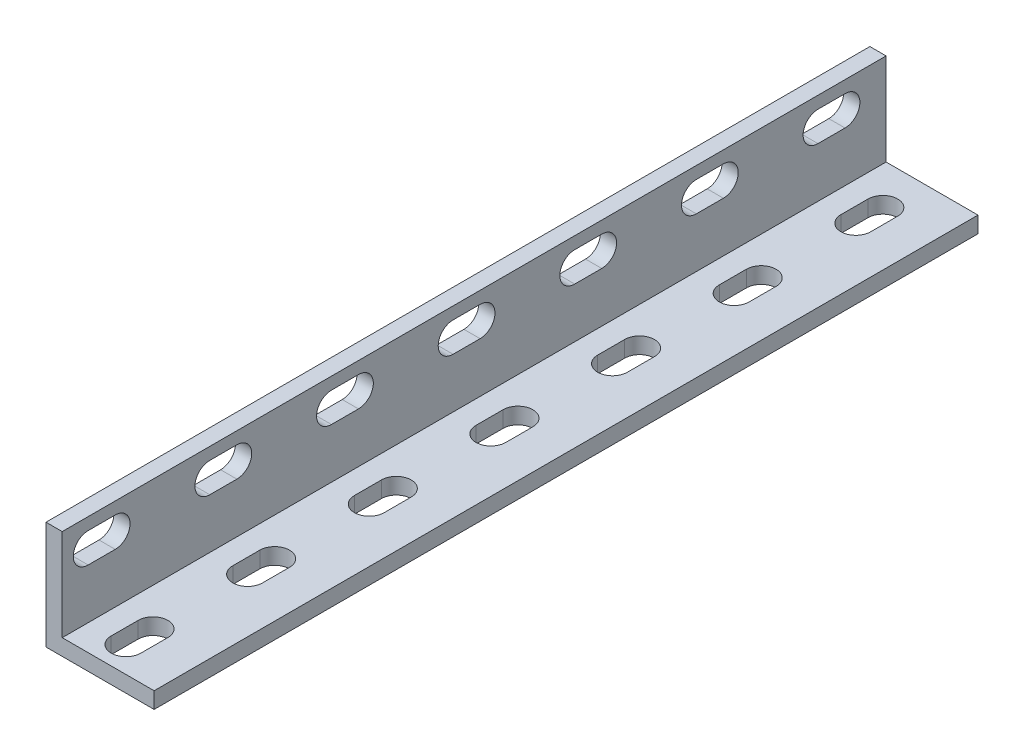
SolidWorks part; units mm, degrees
material "6061 Alloy"
ref_plane "Front Plane" through (0, 0, 0) normal (0, 0, 1) x (1, 0, 0)
ref_plane "Top Plane" through (0, 0, 0) normal (0, 1, 0) x (1, 0, 0)
ref_plane "Right Plane" through (0, 0, 0) normal (1, 0, 0) x (0, 0, -1)
sketch "Sketch1" plane through (0, 0, 0) normal (0, 0, 1) x (1, 0, 0)
  line L0 (0, 20) -> (0, 0)
  line L1 (0, 0) -> (20, 0)
  dimension "D1" = 20
  dimension "D2" = 20
extrude "Extrude-Thin1" add sketch "Sketch1" along normal blind 152.4 thin thin type one direction reverse wall 3
sketch "Sketch2" plane through (0, 3, 0) normal (0, 1, 0) x (1, 0, 0)
  line L0 (10, -147.6) -> (10, -142.6) construction
  line L1 (7.25, -147.6) -> (7.25, -142.6)
  line L2 (12.75, -147.6) -> (12.75, -142.6)
  line L3 (20, -152.4) -> (20, 0) construction
  line L4 (3, -152.4) -> (3, 0) construction
  line L5 (3, -152.4) -> (20, -152.4) construction
  line L6 (10, -120.1) -> (10, -125.1) construction
  line L7 (12.75, -120.1) -> (12.75, -125.1)
  line L8 (7.25, -120.1) -> (7.25, -125.1)
  line L9 (10, -102.6) -> (10, -97.6) construction
  line L10 (7.25, -102.6) -> (7.25, -97.6)
  line L11 (12.75, -102.6) -> (12.75, -97.6)
  arc A0 (7.25, -147.6) -> (12.75, -147.6) centre (10, -147.6) ccw
  arc A1 (12.75, -142.6) -> (7.25, -142.6) centre (10, -142.6) ccw
  arc A2 (12.75, -120.1) -> (7.25, -120.1) centre (10, -120.1) ccw
  arc A3 (7.25, -125.1) -> (12.75, -125.1) centre (10, -125.1) ccw
  arc A4 (7.25, -102.6) -> (12.75, -102.6) centre (10, -102.6) ccw
  arc A5 (12.75, -97.6) -> (7.25, -97.6) centre (10, -97.6) ccw
  point P2 (10, -145.1)
  point P15 (10, -122.6)
  point P20 (10, -100.1)
  point P29 (10, -127.85)
  point P30 (10, -105.35)
  dimension "D1" = 7.25
  dimension "D2" = 4.25
  dimension "D3" = 4.8
  dimension "D4" = 9.8
  dimension "D5" = 24.55
  dimension "D6" = 47.05
extrude "Cut-Extrude1" cut sketch "Sketch2" against normal blind 3
sketch "Sketch3" plane through (3, 0, 0) normal (1, 0, 0) x (0, 0, -1)
  line L0 (-147.6, 15) -> (-142.6, 15) construction
  line L1 (-147.6, 17.75) -> (-142.6, 17.75)
  line L2 (-147.6, 12.25) -> (-142.6, 12.25)
  line L3 (-125.1, 15) -> (-120.1, 15) construction
  line L4 (-125.1, 17.75) -> (-120.1, 17.75)
  line L5 (-125.1, 12.25) -> (-120.1, 12.25)
  line L6 (-102.6, 15) -> (-97.6, 15) construction
  line L7 (-102.6, 17.75) -> (-97.6, 17.75)
  line L8 (-102.6, 12.25) -> (-97.6, 12.25)
  line L9 (-97.6, 3) -> (-102.6, 3) construction
  line L10 (-152.4, 20) -> (0, 20) construction
  arc A0 (-147.6, 17.75) -> (-147.6, 12.25) centre (-147.6, 15) ccw
  arc A1 (-142.6, 12.25) -> (-142.6, 17.75) centre (-142.6, 15) ccw
  arc A2 (-125.1, 17.75) -> (-125.1, 12.25) centre (-125.1, 15) ccw
  arc A3 (-120.1, 12.25) -> (-120.1, 17.75) centre (-120.1, 15) ccw
  arc A4 (-102.6, 17.75) -> (-102.6, 12.25) centre (-102.6, 15) ccw
  arc A5 (-97.6, 12.25) -> (-97.6, 17.75) centre (-97.6, 15) ccw
  point P2 (-145.1, 15)
  point P7 (-122.6, 15)
  point P14 (-100.1, 15)
  dimension "D1" = 2.75
  dimension "D2" = 0
  dimension "D3" = 0
  dimension "D4" = 2.25
  dimension "D5" = 17.5
extrude "Cut-Extrude2" cut sketch "Sketch3" against normal blind 3
pattern_linear "LPattern1" count 4 spacing 45 along (0, 0, -1) of "Cut-Extrude1"
pattern_linear "LPattern2" count 4 spacing 45 along (0, 0, -1) of "Cut-Extrude2"
